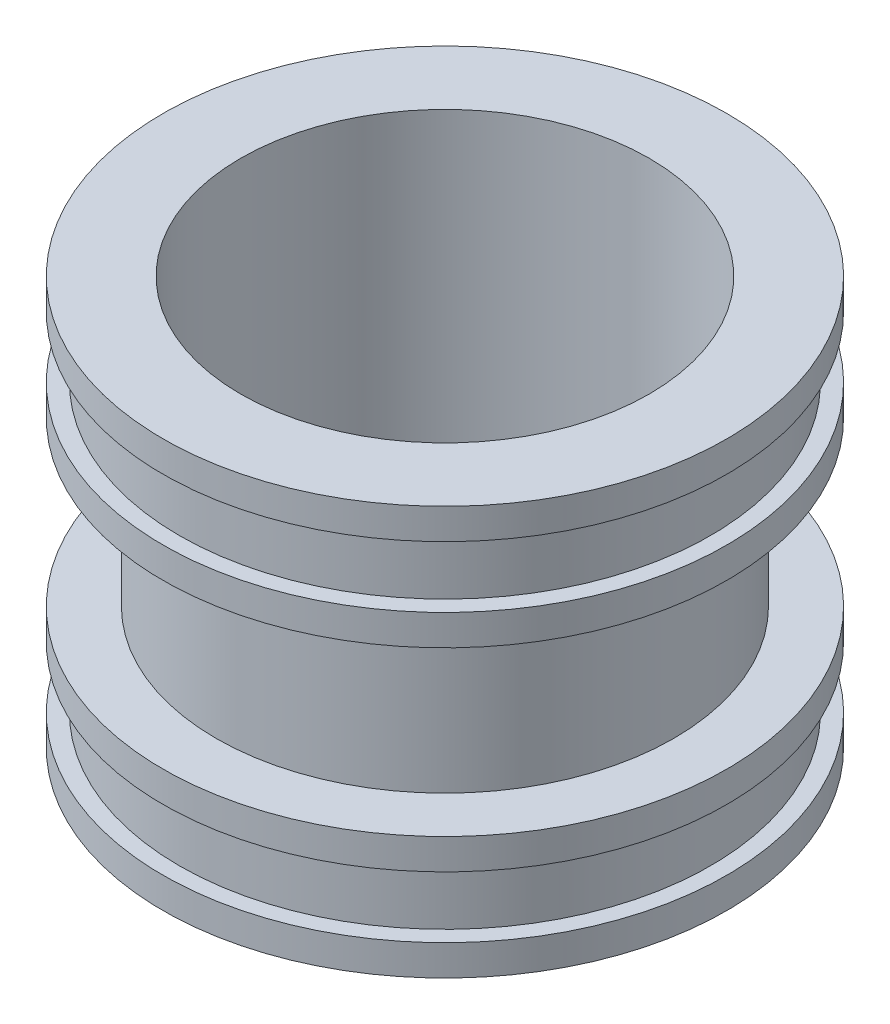
SolidWorks part; units mm, degrees
material "AISI 1020"
ref_plane "Plano frontal" through (0, 0, 0) normal (0, 0, 1) x (1, 0, 0)
ref_plane "Plano superior" through (0, 0, 0) normal (0, 1, 0) x (1, 0, 0)
ref_plane "Plano direito" through (0, 0, 0) normal (1, 0, 0) x (0, 0, -1)
sketch "Esboço1" plane through (0, 0, 0) normal (0, 0, 1) x (1, 0, 0)
  line L0 (0, 0) -> (0, 327.1613) construction
  line L1 (0, 0) -> (502.3995, 0) construction
  line L2 (50, 100) -> (69, 100)
  line L3 (69, 100) -> (69, 92.5)
  line L4 (69, 70) -> (56, 70)
  line L5 (56, 70) -> (56, 30)
  line L6 (56, 30) -> (69, 30)
  line L7 (69, 30) -> (69, 22.5)
  line L8 (69, 0) -> (50, 0)
  line L9 (50, 0) -> (50, 100)
  line L10 (69, 92.5) -> (65, 92.5)
  line L11 (65, 92.5) -> (65, 77.5)
  line L12 (65, 77.5) -> (69, 77.5)
  line L13 (50, 50) -> (69, 50) construction
  line L14 (69, 77.5) -> (69, 70)
  line L15 (65, 22.5) -> (69, 22.5)
  line L16 (65, 7.5) -> (65, 22.5)
  line L17 (69, 7.5) -> (65, 7.5)
  line L18 (69, 7.5) -> (69, 0)
  point P22 (56, 50)
  dimension "D1" = 100
  dimension "D2" = 4
  dimension "D3" = 15
  dimension "D4" = 30
  dimension "250" = 138
  dimension "D6" = 6
  dimension "D7" = 100
revolve "Revolução1" add sketch "Esboço1" angle 360 about L0
